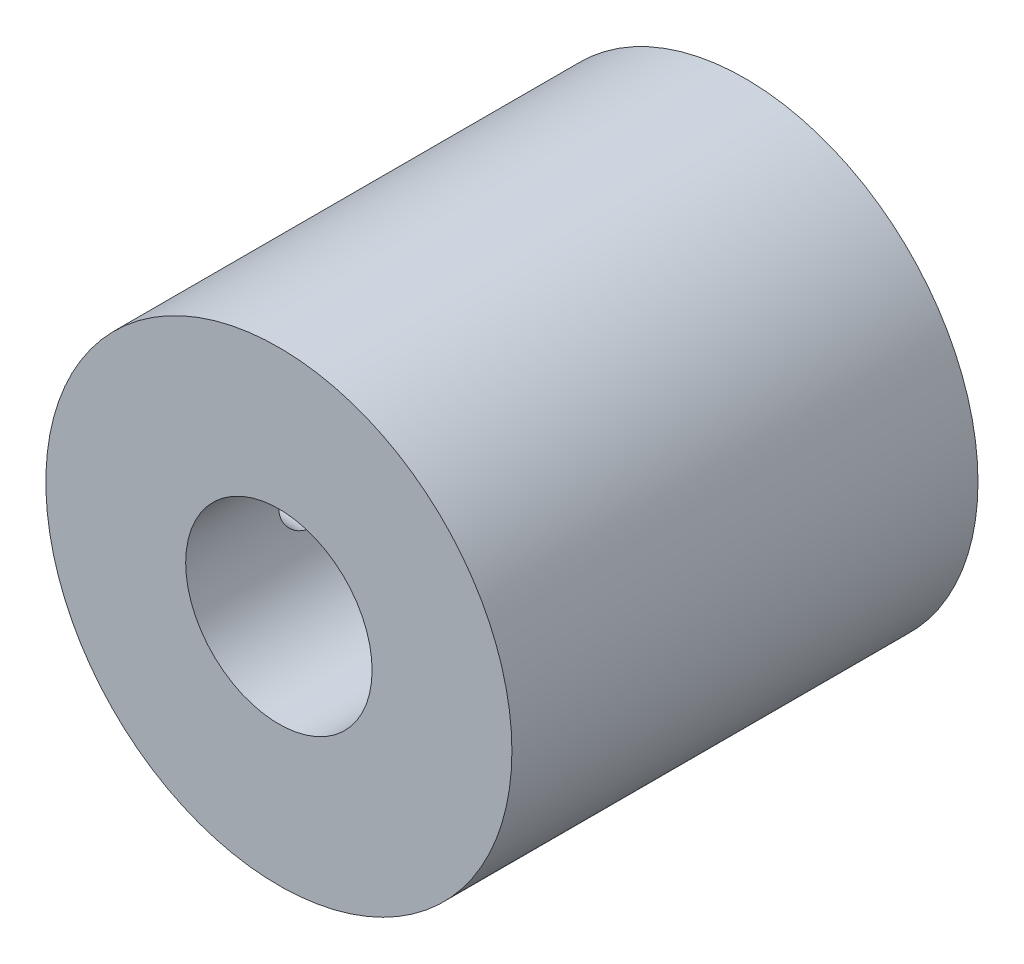
SolidWorks part; units mm, degrees
ref_plane "Alzado" through (0, 0, 0) normal (0, 0, 1) x (1, 0, 0)
ref_plane "Planta" through (0, 0, 0) normal (0, 1, 0) x (1, 0, 0)
ref_plane "Vista lateral" through (0, 0, 0) normal (1, 0, 0) x (0, 0, -1)
sketch "Croquis1" plane through (0, 0, 0) normal (0, 0, 1) x (1, 0, 0)
  circle A0 centre (0, 0) radius 12.5
extrude "Saliente-Extruir1" add sketch "Croquis1" along normal mid plane 25 contours A0
sketch "Croquis2" plane through (0, 0, 12.5) normal (0, 0, 1) x (1, 0, 0)
  circle A0 centre (0, 0) radius 5
extrude "Cortar-Extruir1" cut sketch "Croquis2" against normal blind 25 contours A0
sketch "Croquis3" plane through (0, 0, 0) normal (1, 0, 0) x (0, 0, -1)
  line L0 (0, 0) -> (-6, 0) construction
  line L1 (0, 0) -> (6, 0) construction
  circle A0 centre (-6, 0) radius 1.5
  circle A1 centre (6, 0) radius 1.5
extrude "Cortar-Extruir2" cut sketch "Croquis3" against normal up to next
